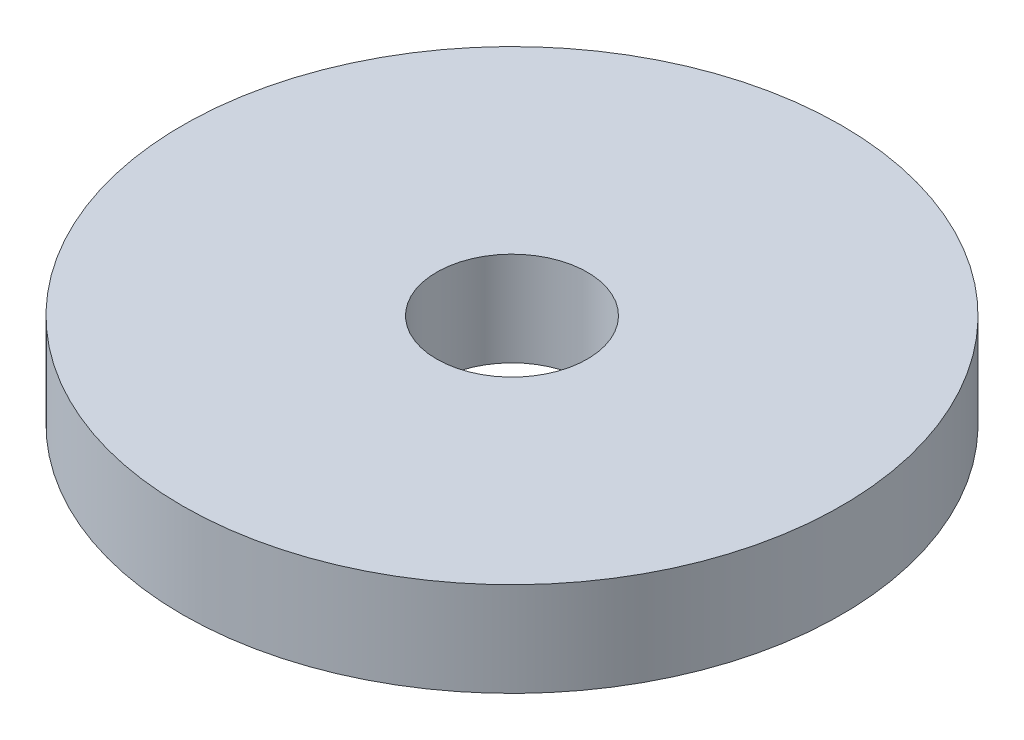
SolidWorks part; units mm, degrees
ref_plane "Front Plane" through (0, 0, 0) normal (0, 0, 1) x (1, 0, 0)
ref_plane "Top Plane" through (0, 0, 0) normal (0, 1, 0) x (1, 0, 0)
ref_plane "Right Plane" through (0, 0, 0) normal (1, 0, 0) x (0, 0, -1)
sketch "Sketch1" plane through (0, 0, 0) normal (0, 1, 0) x (1, 0, 0)
  circle A0 centre (0, 0) radius 1.6
  circle A1 centre (0, 0) radius 7
  dimension "D1" = 3.2
  dimension "D2" = 14
extrude "Boss-Extrude1" add sketch "Sketch1" along normal blind 2
